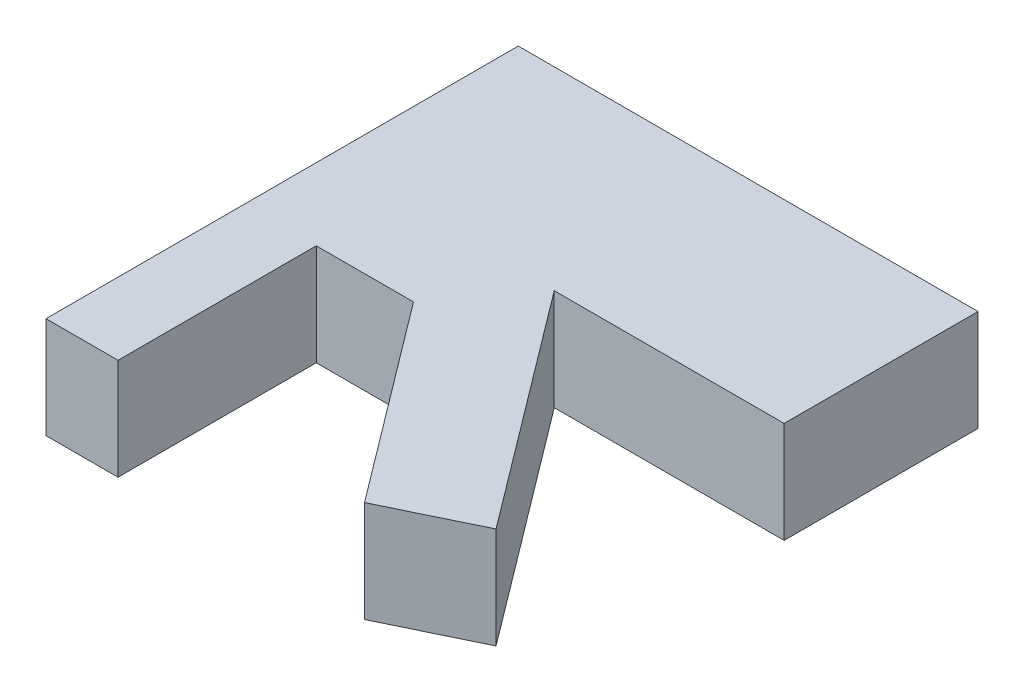
SolidWorks part; units mm, degrees
ref_plane "Front Plane" through (0, 0, 0) normal (0, 0, 1) x (1, 0, 0)
ref_plane "Top Plane" through (0, 0, 0) normal (0, 1, 0) x (1, 0, 0)
ref_plane "Right Plane" through (0, 0, 0) normal (1, 0, 0) x (0, 0, -1)
sketch "Sketch1" plane through (0, 0, 0) normal (0, 1, 0) x (1, 0, 0)
  line L0 (0, 0) -> (0, 46.6081)
  line L1 (0, 46.6081) -> (45.378, 46.6081)
  line L2 (45.378, 46.6081) -> (45.378, 27.4728)
  line L3 (45.378, 27.4728) -> (22.689, 27.4728)
  line L4 (22.689, 27.4728) -> (40.1841, 4.2371)
  line L5 (40.1841, 4.2371) -> (31.4365, 0)
  line L6 (31.4365, 0) -> (16.7038, 19.567)
  line L7 (16.7038, 19.567) -> (7.1074, 19.567)
  line L8 (7.1074, 19.567) -> (7.1074, 0)
  line L9 (7.1074, 0) -> (0, 0)
extrude "Boss-Extrude1" add sketch "Sketch1" along normal blind 10
